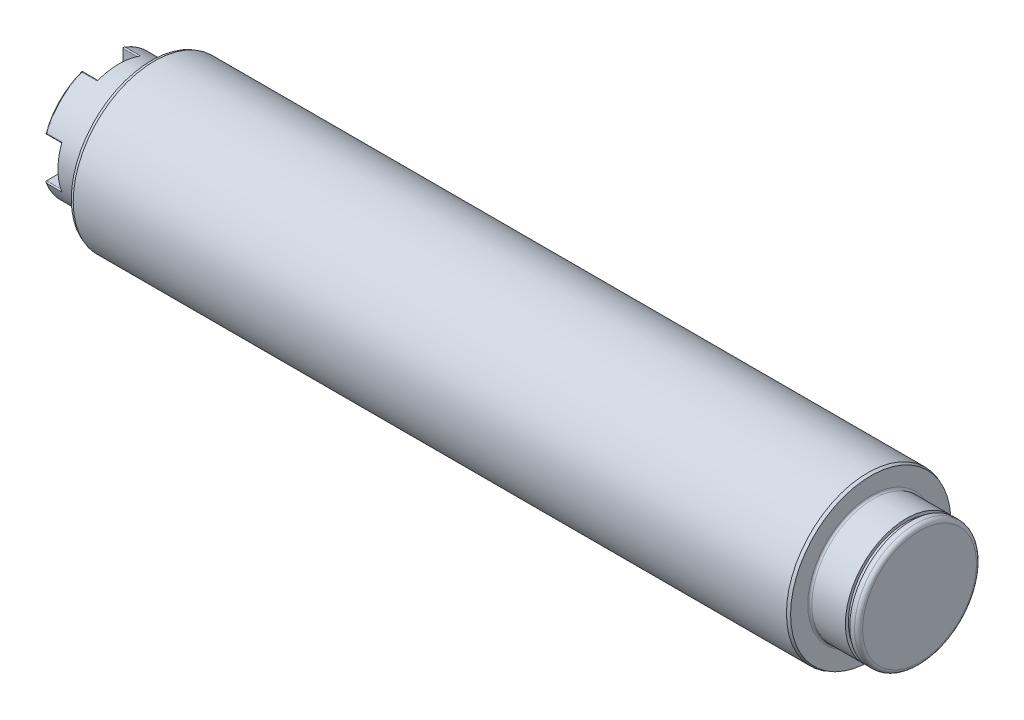
SolidWorks part; units mm, degrees
ref_plane "Front" through (0, 0, 0) normal (0, 0, 1) x (1, 0, 0)
ref_plane "Top" through (0, 0, 0) normal (0, 1, 0) x (1, 0, 0)
ref_plane "Right" through (0, 0, 0) normal (1, 0, 0) x (0, 0, -1)
sketch "Sketch1" plane through (0, 0, 0) normal (0, 0, 1) x (1, 0, 0)
  line L0 (-283, 0) -> (11.2597, 0) construction
  line L1 (-201, 20) -> (-201, 30)
  line L2 (-201, 20) -> (-193, 20)
  line L3 (-193, 20) -> (-193, 8.5)
  line L4 (-201, 30) -> (-177, 30)
  line L6 (194.5, 30) -> (194.5, 28.5)
  line L7 (194.5, 28.5) -> (196.65, 28.5)
  line L8 (201, 0) -> (201, 28)
  line L9 (-146.794, 0) -> (201, 0)
  line L10 (-177, 30) -> (-177, 39.454)
  line L11 (-175.5, 40) -> (175.5, 40)
  line L12 (177, 30) -> (194.5, 30)
  line L13 (-177, 39.454) -> (-175.5, 40)
  line L14 (177, 39.454) -> (175.5, 40)
  line L15 (177, 30) -> (177, 39.454)
  line L16 (-193, 8.5) -> (-183, 8.5)
  line L17 (-183, 8.5) -> (-182.0987, 7)
  line L18 (-182.0987, 7) -> (-151, 7)
  line L19 (-151, 7) -> (-146.794, 0)
  line L20 (196.65, 28.5) -> (196.65, 30)
  line L21 (196.65, 30) -> (199, 30)
  arc A0 (201, 28) -> (199, 30) centre (199, 28) ccw
  point P27 (201, 30)
  dimension "D18" = 2
  dimension "D1" = 402
  dimension "D2" = 24
  dimension "D3" = 8
  dimension "D4" = 40
  dimension "D5" = 60
  dimension "D6" = 80
  dimension "D7" = 17
  dimension "D8" = 20
  dimension "D9" = 1.5
  dimension "D10" = 14
  dimension "D11" = 59
  dimension "D12" = 59
  dimension "D13" = 10
  dimension "D14" = 42
  dimension "D15" = 6.5
  dimension "D16" = 2.15
  dimension "D17" = 57
  dimension "D19" = 354
  dimension "D20" = 17.5
  dimension "D21" = 201
revolve "Base-Revolve" add sketch "Sketch1" angle 360 about L0
cosmetic thread "Cosmetic Thread2" parameters "D1"=24.1, "D2"=16
fillet "R1 runding" radius 1 2 edges at (177, 0, 30) (-177, 0, 30)
sketch "Sketch3" plane through (-201, 0, 0) normal (-1, 0, 0) x (0, 0, 1)
  line L0 (0, 0) -> (30, 0) construction
  line L1 (0, 0) -> (0, 30) construction
  line L2 (10, 28.2843) -> (10, 17.3205)
  line L3 (-10, 28.2843) -> (-10, 17.3205)
  line L4 (17.3205, 10) -> (28.2843, 10)
  line L5 (17.3205, -10) -> (28.2843, -10)
  line L6 (-17.3205, -10) -> (-28.2843, -10)
  line L7 (-17.3205, 10) -> (-28.2843, 10)
  line L8 (-10, -28.2843) -> (-10, -17.3205)
  line L9 (10, -28.2843) -> (10, -17.3205)
  circle A0 centre (0, 0) radius 20 construction
  circle A1 centre (0, 0) radius 30 construction
  arc A2 (17.3205, -10) -> (17.3205, 10) centre (0, 0) ccw
  arc A3 (28.2843, -10) -> (28.2843, 10) centre (0, 0) ccw
  arc A4 (-10, -17.3205) -> (10, -17.3205) centre (0, 0) ccw
  arc A5 (-10, -28.2843) -> (10, -28.2843) centre (0, 0) ccw
  arc A6 (-28.2843, 10) -> (-28.2843, -10) centre (0, 0) ccw
  arc A7 (-17.3205, 10) -> (-17.3205, -10) centre (0, 0) ccw
  arc A8 (10, 17.3205) -> (-10, 17.3205) centre (0, 0) ccw
  arc A9 (10, 28.2843) -> (-10, 28.2843) centre (0, 0) ccw
  dimension "D1" = 20
  dimension "D2" = 20
extrude "Affræsning" cut sketch "Sketch3" against normal blind 8
fillet "R0.5 rundinger" radius 0.5 24 edges at (-197, -10, 17.3205) (-197, -17.3205, 10) (-197, 10, -28.2843) (-197, 10, 17.3205) (-197, 17.3205, 10) (-197, -10, -28.2843) (-197, -10, -17.3205) (-197, -17.3205, -10) (-197, -28.2843, -10) (-197, -28.2843, 10) (-197, -10, 28.2843) (-197, 28.2843, 10) (-197, 10, 28.2843) (-197, 10, -17.3205) (-197, 28.2843, -10) (-197, 17.3205, -10) (-201, 21.2132, -21.2132) (-201, 21.2132, 21.2132) (-201, -21.2132, 21.2132) (-201, -21.2132, -21.2132) (-201, 14.1421, 14.1421) (-201, -14.1421, 14.1421) (-201, -14.1421, -14.1421) (-201, 14.1421, -14.1421)
